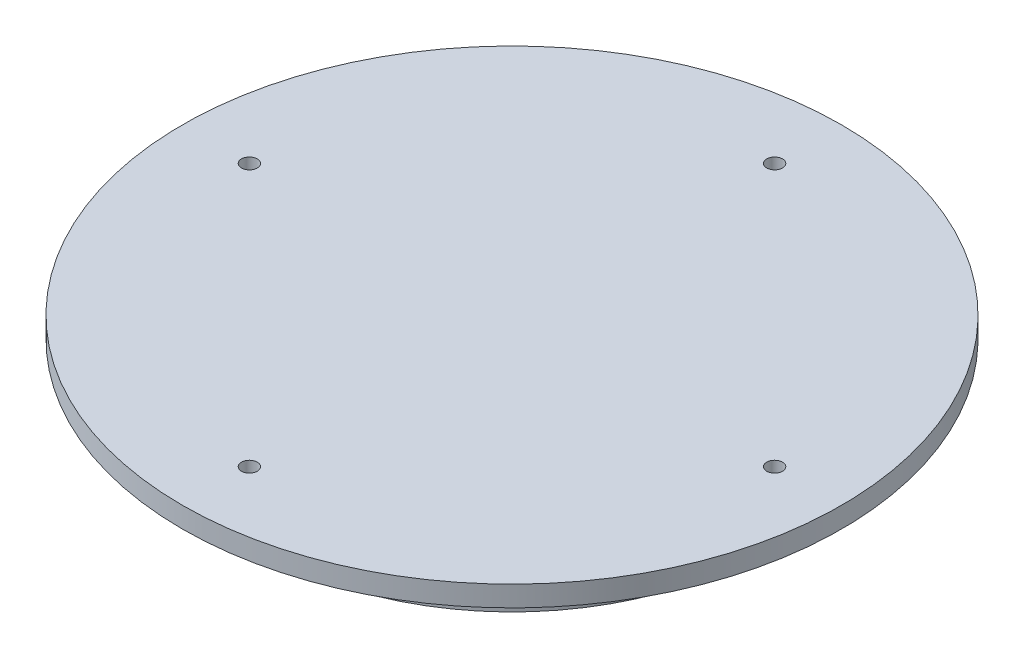
SolidWorks part; units mm, degrees
material "Acrylic (Medium-high impact)"
ref_plane "Front Plane" through (0, 0, 0) normal (0, 0, 1) x (1, 0, 0)
ref_plane "Top Plane" through (0, 0, 0) normal (0, 1, 0) x (1, 0, 0)
ref_plane "Right Plane" through (0, 0, 0) normal (1, 0, 0) x (0, 0, -1)
sketch "Sketch1" plane through (0, 0, 0) normal (0, 1, 0) x (1, 0, 0)
  circle A0 centre (0, 0) radius 38.1 construction
  circle A1 centre (0, 0) radius 50.8
  dimension "D1" = 76.2
  dimension "D2" = 101.6
extrude "Boss-Extrude1" add sketch "Sketch1" along normal blind 3.175
sketch "Sketch2" plane through (0, 0, 0) normal (0, -1, 0) x (1, 0, 0)
  circle A0 centre (0, 0) radius 38.1
  dimension "D1" = 76.2
extrude "Boss-Extrude2" add sketch "Sketch2" along normal blind 9.525
hole_wizard "#2 Clearance Hole1" positions "Sketch4" profile "Sketch3" hole size "#2" standard "Ansi Inch"
sketch "Sketch4" plane through (0, 3.175, 0) normal (0, 1, 0) x (-1, 0, 0)
  line L0 (0, -50.8) -> (0, 50.8) construction
  line L2 (50.8, 0) -> (-50.8, 0) construction
  circle A0 centre (0, 0) radius 50.8 construction
  circle A1 centre (0, 0) radius 40.4813
  point P0 (0, -40.4812)
  point P1 (-40.4812, 0)
  point P3 (40.4812, 0)
  point P5 (0, 40.4812)
  dimension "D1" = 80.9625
sketch "Sketch3" plane through (0, 3.175, -40.4812) normal (1, 0, 0) x (0, 0, 1)
  line L0 (0, 0) -> (0, 26.1326)
  line L1 (0, 26.1326) -> (1.2192, 25.4)
  line L2 (1.2192, 25.4) -> (1.2192, 0)
  line L5 (1.2192, 0) -> (0, 0)
  line L10 (0, 26.1326) -> (-1.2192, 25.4) construction
  line L11 (0, -6.35) -> (0, 107.95) construction
  dimension "Hole Dia." = 2.4384
  dimension "Hole Depth" = 25.4
  dimension "Drill Angle" = 118
